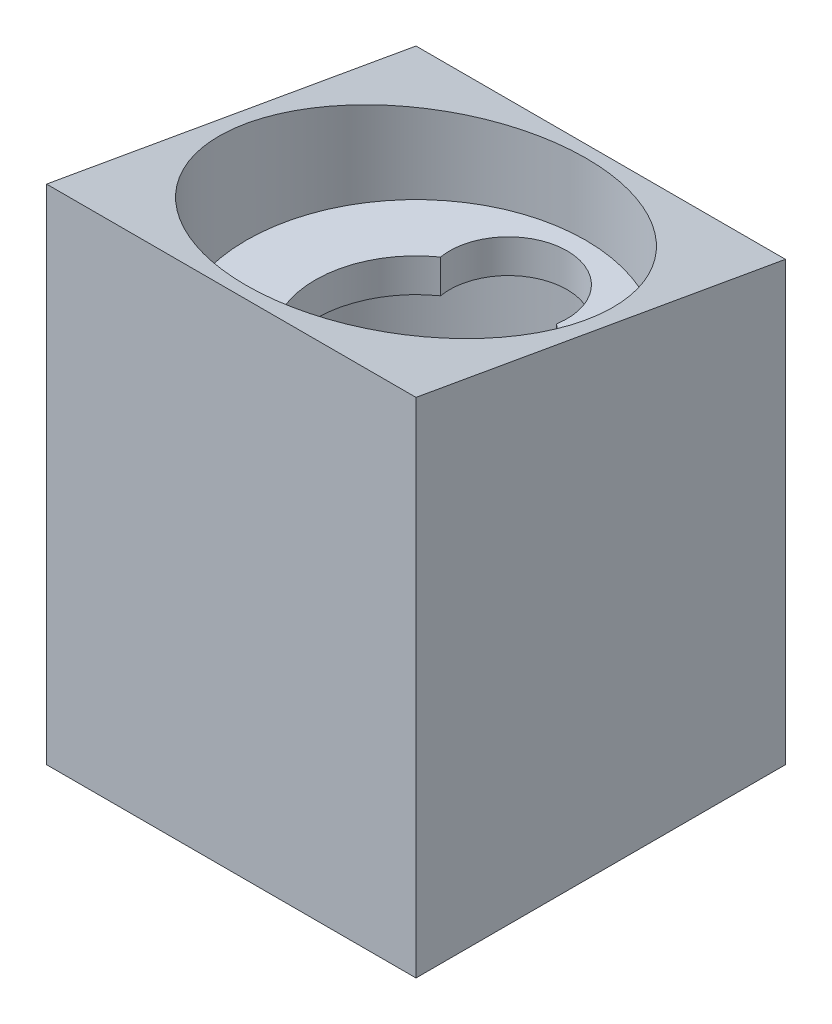
SolidWorks part; units mm, degrees
ref_plane "Front Plane" through (0, 0, 0) normal (0, 0, 1) x (1, 0, 0)
ref_plane "Top Plane" through (0, 0, 0) normal (0, 1, 0) x (1, 0, 0)
ref_plane "Right Plane" through (0, 0, 0) normal (1, 0, 0) x (0, 0, -1)
sketch "Sketch2" plane through (0, 0, 0) normal (0, 1, 0) x (1, 0, 0)
  circle A0 centre (0, 0) radius 10.1
  arc A3 (-3.4498, 4.9091) -> (3.4498, 4.9091) centre (0, 5.5) cw
  arc A4 (-3.4498, 4.9091) -> (3.4498, 4.9091) centre (0, 0) ccw
  point P3 (-3.3181, 4.3864)
  dimension "D1" = 20.2
  dimension "D2" = 5.5
  dimension "D3" = 6
  dimension "D4" = 3.5
extrude "Boss-Extrude1" add sketch "Sketch2" along normal blind 2
sketch "Sketch3" plane through (0, 2, 0) normal (0, 1, 0) x (1, 0, 0)
  line L4 (0, 10.1) -> (0, -10.1) construction
  line L8 (-11, 11) -> (11, 11)
  line L9 (-11, 11) -> (-11, -11)
  line L10 (-11, -11) -> (11, -11)
  line L11 (11, 11) -> (11, -11)
  line L12 (-11, 11) -> (11, -11) construction
  line L13 (-11, -11) -> (11, 11) construction
  circle A0 centre (0, 0) radius 10.1 construction
  circle A3 centre (0, 0) radius 10.125
  point P0 (0, 0)
  dimension "D3" = 20.25
  dimension "D1" = 22
  dimension "D2" = 22
extrude "Boss-Extrude2" add sketch "Sketch3" along normal blind 8 and the other way blind 22
sketch "Sketch5" plane through (0, -20, 0) normal (0, -1, 0) x (-1, 0, 0)
  line L0 (11, -11) -> (9.25, -11) construction
  line L1 (11, -11) -> (-11, -11) construction
  line L2 (9.25, -11) -> (9.25, -9) construction
  line L3 (0, -11) -> (0, 11) construction
  line L4 (-11, 11) -> (11, 11) construction
  line L5 (11, 0) -> (-11, 0) construction
  line L6 (11, 11) -> (11, -11) construction
  line L7 (-11, -11) -> (-11, 11) construction
  circle A0 centre (9.25, -9) radius 0.985
  circle A1 centre (9.25, 9) radius 0.985
  circle A2 centre (-9.25, 9) radius 0.985
  circle A3 centre (-9.25, -9) radius 0.985
  dimension "D1" = 1.97
  dimension "D2" = 1.75
  dimension "D3" = 2
extrude "Cut-Extrude2" cut sketch "Sketch5" against normal blind 6
sketch "Sketch6" plane through (11, 0, 0) normal (1, 0, 0) x (0, 0, -1)
  line L0 (11, 6.0629) -> (-11, 6.0629) construction
  line L1 (11, -20) -> (11, 10) construction
  line L3 (-11, -20) -> (-11, 10) construction
  line L4 (11, 6.0629) -> (-11, 9.9421)
  line L5 (11, 6.0629) -> (11, 10)
  line L6 (11, 10) -> (-11, 10)
  line L7 (-11, 10) -> (-11, 9.9421)
  dimension "D1" = 10
extrude "Cut-Extrude3" cut sketch "Sketch6" against normal through all contours L7 L4 L5 L6
